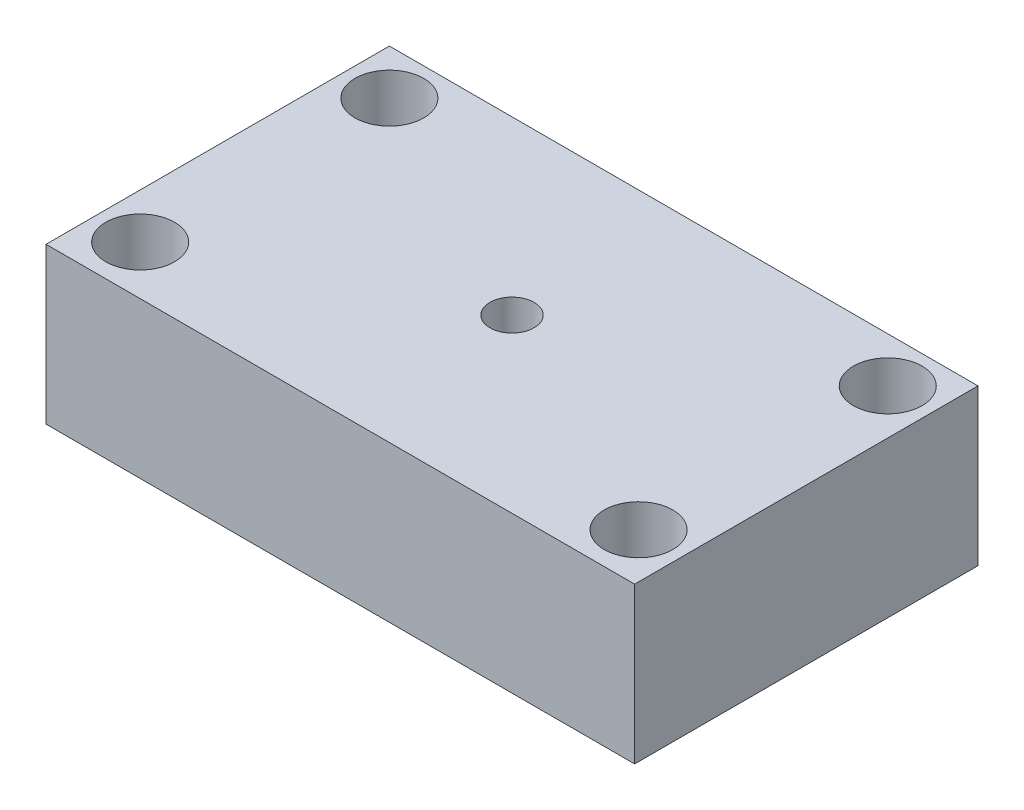
SolidWorks part; units mm, degrees
ref_plane "Front Plane" through (0, 0, 0) normal (0, 0, 1) x (1, 0, 0)
ref_plane "Top Plane" through (0, 0, 0) normal (0, 1, 0) x (1, 0, 0)
ref_plane "Right Plane" through (0, 0, 0) normal (1, 0, 0) x (0, 0, -1)
sketch "Sketch1" plane through (0, 0, 0) normal (0, 1, 0) x (1, 0, 0)
  line L0 (4.6, 30.4) -> (0, 30.4) construction
  line L1 (0, 0) -> (60, 0)
  line L2 (0, 0) -> (0, 35)
  line L3 (0, 35) -> (60, 35)
  line L4 (60, 0) -> (60, 35)
  line L5 (4.6, 30.4) -> (55.4, 30.4) construction
  line L6 (4.6, 30.4) -> (4.6, 5) construction
  line L7 (4.6, 5) -> (55.4, 5) construction
  line L8 (55.4, 30.4) -> (55.4, 5) construction
  line L9 (4.6, 30.4) -> (4.6, 35) construction
  circle A0 centre (4.6, 30.4) radius 3.5
  circle A1 centre (55.4, 30.4) radius 3.5
  circle A2 centre (4.6, 5) radius 3.5
  circle A3 centre (55.4, 5) radius 3.5
  circle A4 centre (30, 17.5) radius 2.25
  point P13 (30, 30.4)
  point P14 (30, 35)
  point P20 (60, 17.5)
  dimension "D5" = 7
  dimension "D6" = 4.5
  dimension "D1" = 60
  dimension "D2" = 35
  dimension "D3" = 50.8
  dimension "D4" = 25.4
extrude "Boss-Extrude1" add sketch "Sketch1" along normal blind 15.875
